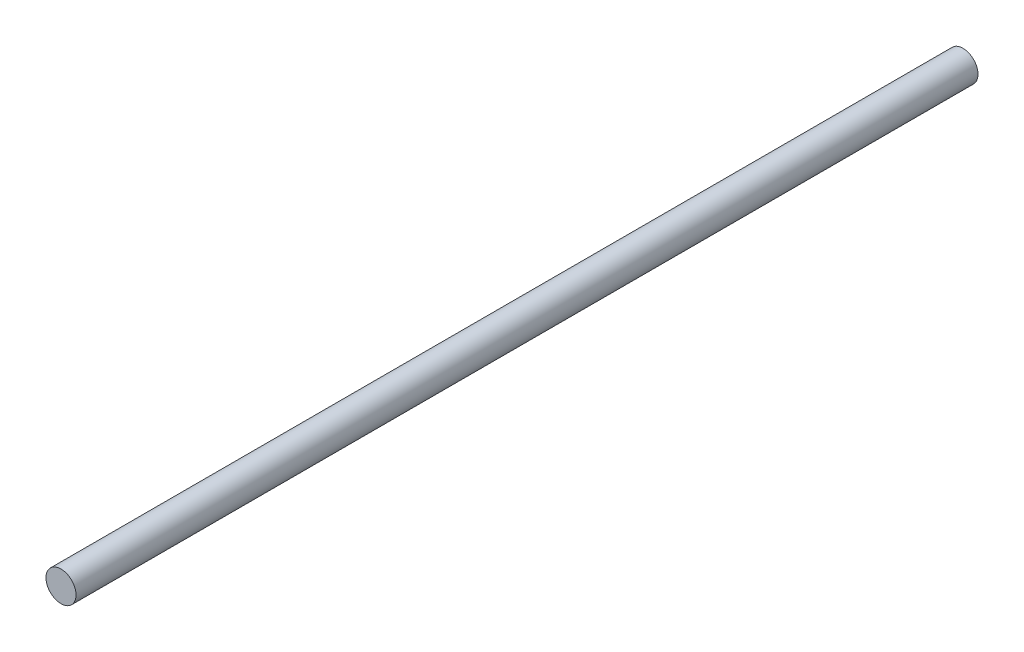
SolidWorks part; units mm, degrees
ref_plane "前视基准面" through (0, 0, 0) normal (0, 0, 1) x (1, 0, 0)
ref_plane "上视基准面" through (0, 0, 0) normal (0, 1, 0) x (1, 0, 0)
ref_plane "右视基准面" through (0, 0, 0) normal (1, 0, 0) x (0, 0, -1)
other "Configuration Table"
sketch "草图1" plane through (0, 0, 0) normal (0, 0, 1) x (1, 0, 0)
  circle A0 centre (0, 0) radius 5
  dimension "D1" = 10
extrude "凸台-拉伸1" add sketch "草图1" along normal blind 300
